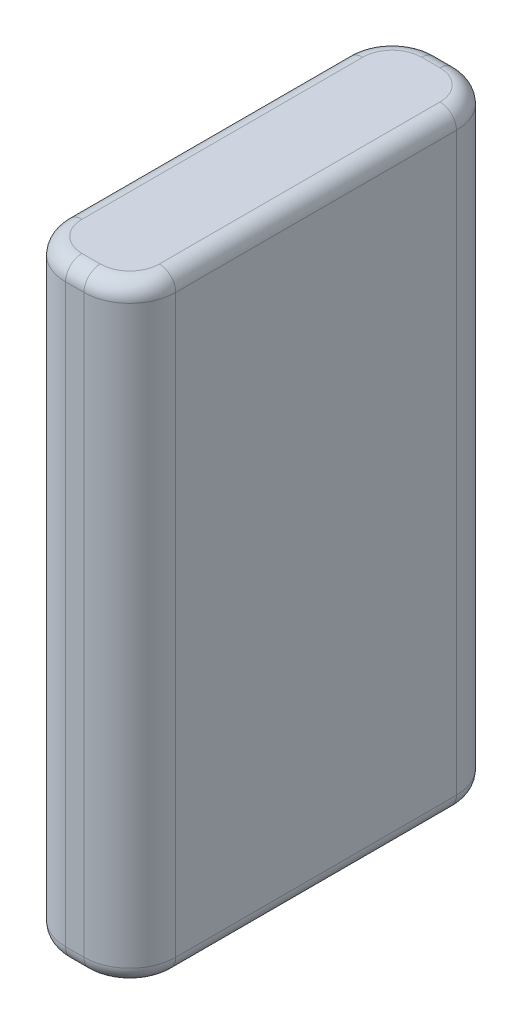
SolidWorks part; units mm, degrees
ref_plane "Front Plane" through (0, 0, 0) normal (0, 0, 1) x (1, 0, 0)
ref_plane "Top Plane" through (0, 0, 0) normal (0, 1, 0) x (1, 0, 0)
ref_plane "Right Plane" through (0, 0, 0) normal (1, 0, 0) x (0, 0, -1)
sketch "Sketch1" plane through (0, 0, 0) normal (0, 1, 0) x (1, 0, 0)
  line L1 (-4.2, -14.2) -> (4.2, -14.2)
  line L2 (-4.2, -14.2) -> (-4.2, 14.2)
  line L3 (-4.2, 14.2) -> (4.2, 14.2)
  line L4 (4.2, -14.2) -> (4.2, 14.2)
  line L5 (-4.2, -14.2) -> (4.2, 14.2) construction
  line L6 (-4.2, 14.2) -> (4.2, -14.2) construction
  point P0 (0, 0)
  dimension "D1" = 28.4
  dimension "D2" = 8.4
extrude "Boss-Extrude1" add sketch "Sketch1" along normal blind 46.4
fillet "Fillet1" radius 3.5 4 edges at (-4.2, 23.2, -14.2) (4.2, 23.2, -14.2) (4.2, 23.2, 14.2) (-4.2, 23.2, 14.2)
fillet "Fillet2" radius 1.25 16 edges at (3.1749, 46.4, -13.1749) (4.2, 46.4, 0) (3.1749, 46.4, 13.1749) (0, 46.4, 14.2) (-3.1749, 46.4, 13.1749) (-4.2, 46.4, 0) (-3.1749, 46.4, -13.1749) (0, 46.4, -14.2) (-3.1749, 0, 13.1749) (0, 0, 14.2) (3.1749, 0, 13.1749) (4.2, 0, 0) (3.1749, 0, -13.1749) (0, 0, -14.2) (-3.1749, 0, -13.1749) (-4.2, 0, 0)
